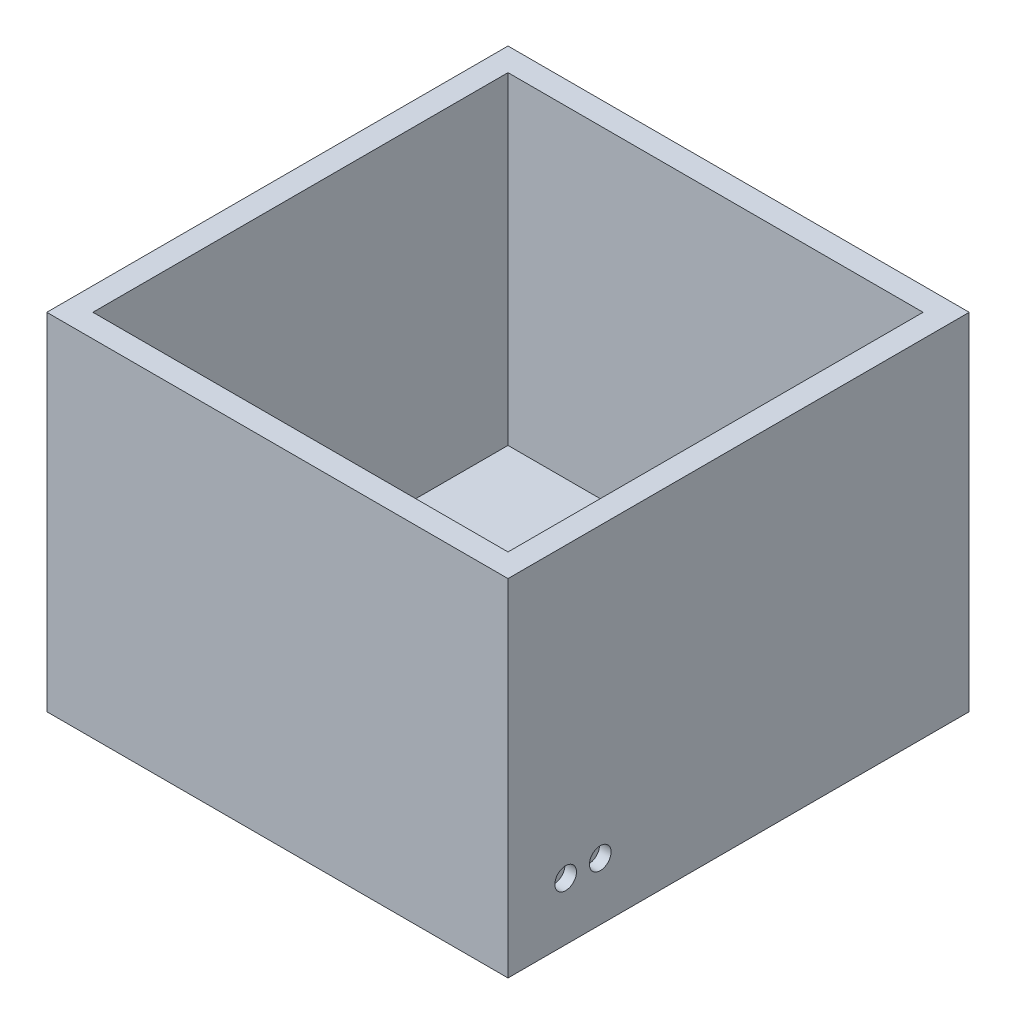
SolidWorks part; units mm, degrees
ref_plane "Front Plane" through (0, 0, 0) normal (0, 0, 1) x (1, 0, 0)
ref_plane "Top Plane" through (0, 0, 0) normal (0, 1, 0) x (1, 0, 0)
ref_plane "Right Plane" through (0, 0, 0) normal (1, 0, 0) x (0, 0, -1)
sketch "Sketch1" plane through (0, 0, 0) normal (0, 1, 0) x (1, 0, 0)
  line L1 (-97.6923, 58.7474) -> (3.9077, 58.7474)
  line L2 (-97.6923, 58.7474) -> (-97.6923, -42.8526)
  line L3 (-97.6923, -42.8526) -> (3.9077, -42.8526)
  line L4 (3.9077, 58.7474) -> (3.9077, -42.8526)
  dimension "D1" = 101.6
  dimension "D2" = 101.6
extrude "Boss-Extrude1" add sketch "Sketch1" along normal blind 76.2
sketch "Sketch2" plane through (0, 76.2, 0) normal (0, 1, 0) x (1, 0, 0)
  line L0 (3.9077, -42.8526) -> (3.9077, 58.7474) construction
  line L1 (-92.6123, 53.6674) -> (-1.1723, 53.6674)
  line L2 (-92.6123, 53.6674) -> (-92.6123, -37.7726)
  line L3 (-92.6123, -37.7726) -> (-1.1723, -37.7726)
  line L4 (-1.1723, 53.6674) -> (-1.1723, -37.7726)
  line L5 (-97.6923, -42.8526) -> (3.9077, -42.8526) construction
  line L6 (-97.6923, 58.7474) -> (-97.6923, -42.8526) construction
  line L7 (3.9077, 58.7474) -> (-97.6923, 58.7474) construction
  dimension "D1" = 5.08
  dimension "D2" = 5.08
  dimension "D3" = 5.08
  dimension "D4" = 5.08
extrude "Cut-Extrude1" cut sketch "Sketch2" against normal blind 71.12
sketch "Sketch3" plane through (3.9077, 0, 0) normal (1, 0, 0) x (0, 0, -1)
  line L0 (-42.8526, 76.2) -> (-42.8526, 0) construction
  line L1 (-42.8526, 0) -> (58.7474, 0) construction
  circle A0 centre (-30.1526, 12.7) radius 2.3813
  dimension "D1" = 12.7
  dimension "D2" = 12.7
extrude "Cut-Extrude2" cut sketch "Sketch3" against normal blind 2.54
sketch "Sketch4" plane through (1.3677, 0, 0) normal (1, 0, 0) x (0, 0, -1)
  circle A0 centre (-31.4284, 12.7569) radius 0.635
  circle A1 centre (-28.8884, 12.8595) radius 0.635
  point P2 (0, 0)
  point P5 (0, 0)
  point P6 (0, 0)
  point P7 (-31.4284, 12.7569)
  dimension "D1" = 1.27
  dimension "D2" = 2.54
extrude "Cut-Extrude3" cut sketch "Sketch4" against normal blind 2.54
sketch "Sketch6" plane through (3.9077, 0, 0) normal (1, 0, 0) x (0, 0, -1)
  line L0 (-42.8526, 0) -> (58.7474, 0) construction
  line L1 (-42.8526, 76.2) -> (-42.8526, 0) construction
  circle A0 centre (-22.5326, 12.7) radius 2.3813
  dimension "D1" = 4.7625
  dimension "D2" = 12.7
  dimension "D3" = 20.32
extrude "Cut-Extrude5" cut sketch "Sketch6" against normal blind 2.54
sketch "Sketch8" plane through (1.3677, 0, 0) normal (1, 0, 0) x (0, 0, -1)
  circle A0 centre (-23.8225, 12.8437) radius 0.635
  circle A1 centre (-21.2995, 12.8437) radius 0.635
  point P4 (-23.7962, 12.8437)
  point P5 (-23.8225, 12.8437)
extrude "Cut-Extrude7" cut sketch "Sketch8" against normal blind 2.54
